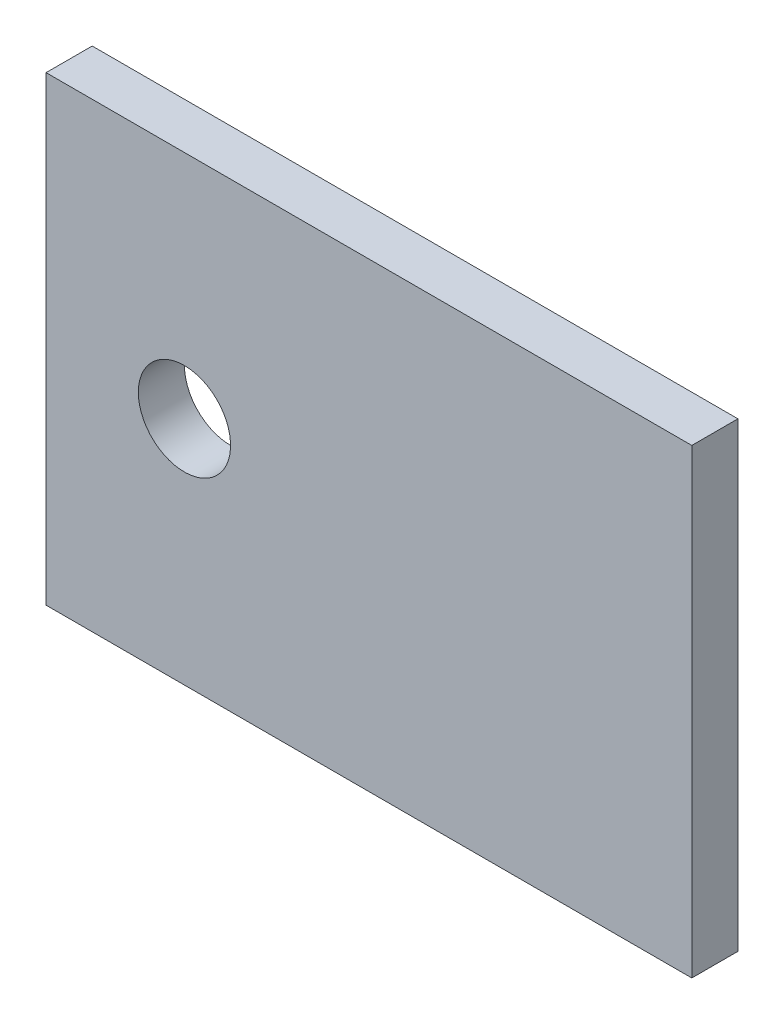
SolidWorks part; units mm, degrees
ref_plane "Plan de face" through (0, 0, 0) normal (0, 0, 1) x (1, 0, 0)
ref_plane "Plan de dessus" through (0, 0, 0) normal (0, 1, 0) x (1, 0, 0)
ref_plane "Plan de droite" through (0, 0, 0) normal (1, 0, 0) x (0, 0, -1)
sketch "Esquisse1" plane through (0, 0, 0) normal (0, 0, 1) x (1, 0, 0)
  line L0 (-35, 0) -> (35, 0)
other "Elément mécano-soudé1"
ref_plane "Plan1" through (-35, 0, 0) normal (1, 0, 0) x (0, 1, 0)
sketch "plat" plane through (-35, 0, 0) normal (1, 0, 0) x (0, 1, 0)
  line L0 (-25, 0) -> (25, 0) construction
  line L1 (-25, 2.5) -> (25, 2.5)
  line L2 (-25, 2.5) -> (-25, -2.5)
  line L3 (-25, -2.5) -> (25, -2.5)
  line L4 (25, 2.5) -> (25, -2.5)
  line L5 (0, 2.5) -> (0, -2.5) construction
  point P8 (0, 0)
  dimension "B" = 50
  dimension "A" = 5
hole_wizard "Diamètre du perçage Ø10.0 (10)1" positions "Esquisse3" profile "Esquisse2" hole size "Ø10.0" standard "Ansi Metric" end condition through all
sketch "Esquisse3" plane through (0, 0, -2.5) normal (0, 0, -1) x (-1, 0, 0)
  line L0 (35, 0) -> (-35, 0) construction
  line L1 (-35, -25) -> (-35, 25) construction
  point P0 (20, 0)
  dimension "D1" = 55
sketch "Esquisse2" plane through (-20, 0, -2.5) normal (1, 0, 0) x (0, 1, 0)
  line L0 (0, 0) -> (0, 5)
  line L1 (0, 5) -> (5, 5)
  line L2 (5, 5) -> (5, 0)
  line L5 (5, 0) -> (0, 0)
  line L11 (0, -6.35) -> (0, 107.95) construction
  dimension "Diamètre du perçage jusqu'au prochain" = 10
  dimension "Profondeur du perçage jusqu'au prochain" = 5
